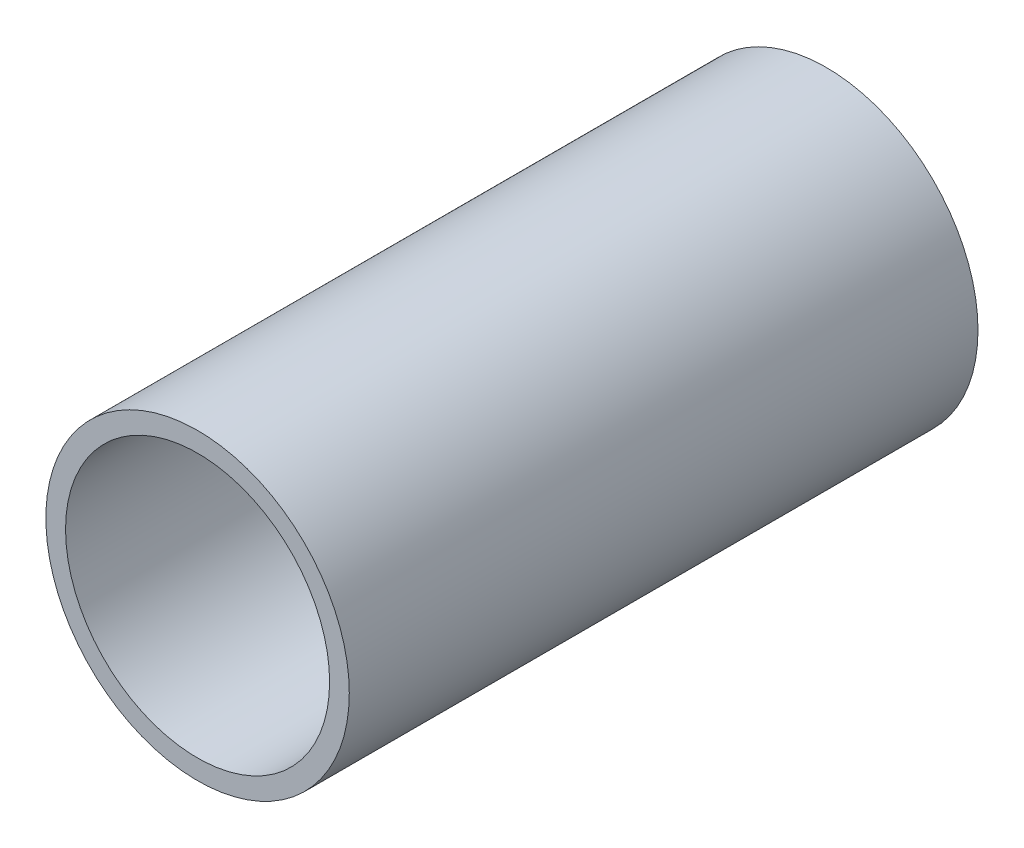
SolidWorks part; units mm, degrees
ref_plane "Alzado" through (0, 0, 0) normal (0, 0, 1) x (1, 0, 0)
ref_plane "Planta" through (0, 0, 0) normal (0, 1, 0) x (1, 0, 0)
ref_plane "Vista lateral" through (0, 0, 0) normal (1, 0, 0) x (0, 0, -1)
sketch "Croquis1" plane through (0, 0, 0) normal (0, 0, 1) x (1, 0, 0)
  circle A0 centre (0, 0) radius 30.165
  circle A1 centre (0, 0) radius 26.25
  dimension "D1" = 52.5
  dimension "D2" = 60.33
extrude "Saliente-Extruir1" add sketch "Croquis1" along normal blind 125
